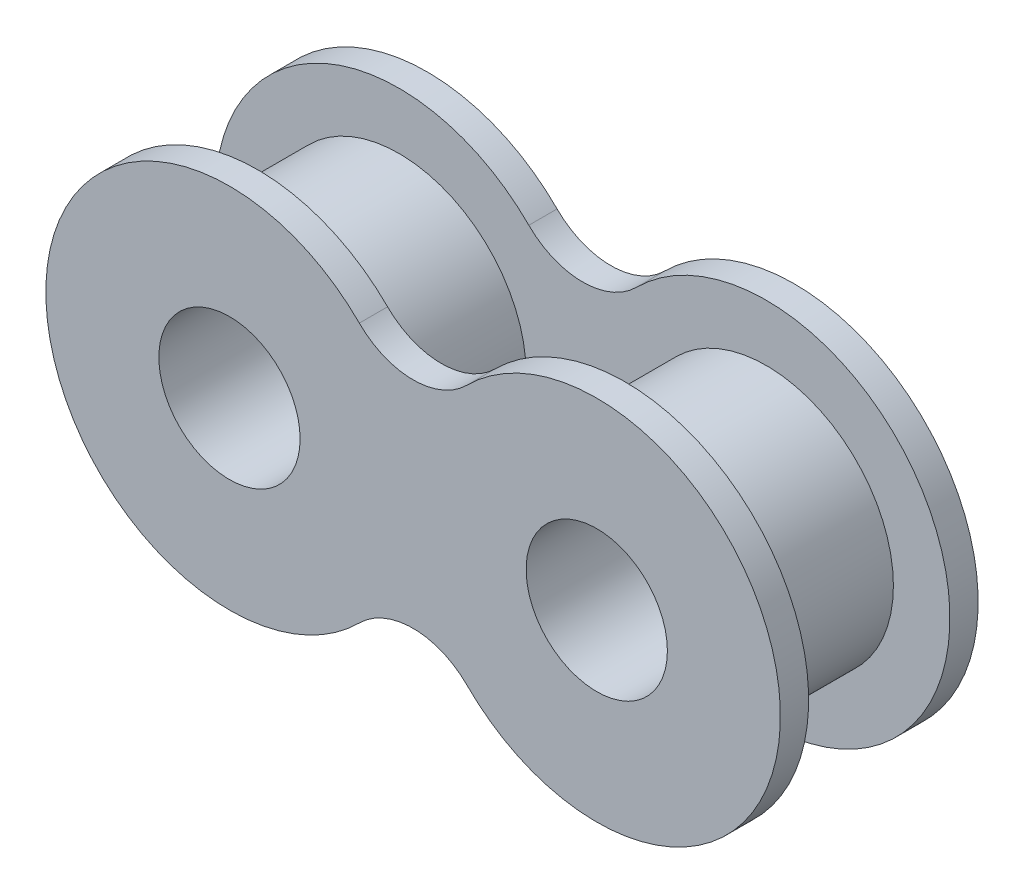
SolidWorks part; units mm, degrees
ref_plane "Alzado" through (0, 0, 0) normal (0, 0, 1) x (1, 0, 0)
ref_plane "Planta" through (0, 0, 0) normal (0, 1, 0) x (1, 0, 0)
ref_plane "Vista lateral" through (0, 0, 0) normal (1, 0, 0) x (0, 0, -1)
sketch "Croquis1" plane through (0, 0, 0) normal (0, 0, 1) x (1, 0, 0)
  line L0 (-6.5, 0) -> (6.5, 0) construction
  line L1 (0, 6.5) -> (0, 3.8076) construction
  line L2 (0, -3.8076) -> (0, -6.5) construction
  arc A0 (-1.9038, 4.5962) -> (-1.9038, -4.5962) centre (-6.5, 0) ccw
  arc A1 (1.9038, -4.5962) -> (1.9038, 4.5962) centre (6.5, 0) ccw
  arc A2 (-1.9038, 4.5962) -> (1.9038, 4.5962) centre (0, 6.5) ccw
  arc A3 (1.9038, -4.5962) -> (-1.9038, -4.5962) centre (0, -6.5) ccw
  circle A4 centre (-6.5, 0) radius 2.5
  circle A5 centre (6.5, 0) radius 2.5
  point P4 (0, 0)
  point P10 (0, 0)
  point P11 (0, 0)
  dimension "D3" = 5
  dimension "D4" = 5
  dimension "D1" = 13
  dimension "D2" = 13
extrude "Saliente-Extruir1" add sketch "Croquis1" along normal blind 1
sketch "Croquis2" plane through (0, 0, 1) normal (0, 0, 1) x (1, 0, 0)
  circle A4 centre (-6.5, 0) radius 2.5
  circle A5 centre (6.5, 0) radius 2.5
  circle A6 centre (6.5, 0) radius 4.5
  circle A7 centre (-6.5, 0) radius 4.5
  dimension "D1" = 2
extrude "Saliente-Extruir2" add sketch "Croquis2" along normal blind 5
ref_plane "Plano1" through (0, 0, 3.5) normal (0, 0, 1) x (1, 0, 0)
mirror "Simetría1" about plane through (0, 0, 3.5) normal (0, 0, 1) of "Saliente-Extruir1"
